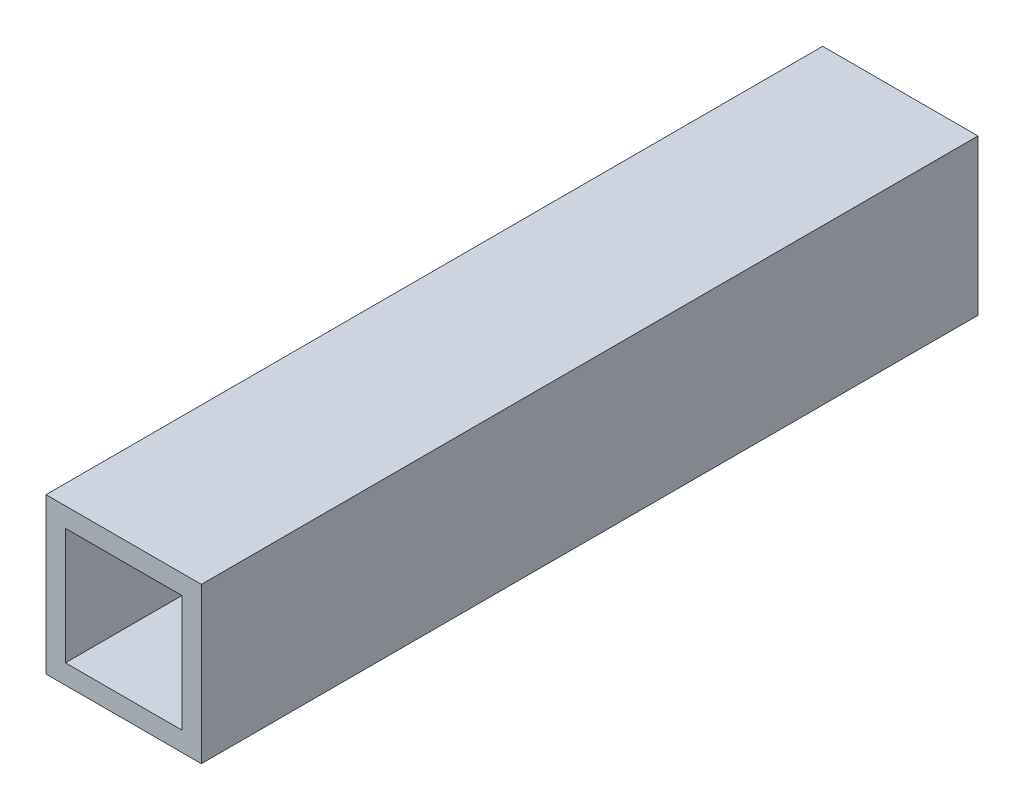
SolidWorks part; units mm, degrees
ref_plane "Front Plane" through (0, 0, 0) normal (0, 0, 1) x (1, 0, 0)
ref_plane "Top Plane" through (0, 0, 0) normal (0, 1, 0) x (1, 0, 0)
ref_plane "Right Plane" through (0, 0, 0) normal (1, 0, 0) x (0, 0, -1)
sketch "Sketch1" plane through (0, 0, 0) normal (0, 0, 1) x (1, 0, 0)
  line L1 (12.7, -12.7) -> (-12.7, -12.7)
  line L2 (12.7, -12.7) -> (12.7, 12.7)
  line L3 (12.7, 12.7) -> (-12.7, 12.7)
  line L4 (-12.7, -12.7) -> (-12.7, 12.7)
  line L5 (12.7, -12.7) -> (-12.7, 12.7) construction
  line L6 (12.7, 12.7) -> (-12.7, -12.7) construction
  point P0 (0, 0)
extrude "Boss-Extrude1" add sketch "Sketch1" along normal blind 127
sketch3d "3DSketch1"
  line L0 (-9.525, -9.525, 127) -> (9.525, -9.525, 127)
  line L1 (9.525, -9.525, 127) -> (9.525, 9.525, 127)
  line L2 (9.525, 9.525, 127) -> (-9.525, 9.525, 127)
  line L3 (-9.525, 9.525, 127) -> (-9.525, -9.525, 127)
  line L4 (-9.525, -9.525, 127) -> (9.525, -9.525, 127)
  line L5 (9.525, -9.525, 127) -> (9.525, 9.525, 127)
  line L6 (9.525, 9.525, 127) -> (-9.525, 9.525, 127)
  line L7 (-9.525, 9.525, 127) -> (-9.525, -9.525, 127)
  dimension "D1" = 3.175
extrude "Cut-Extrude1" cut sketch "3DSketch1" along direction (0, 0, 1) on the side of the normal blind 127 contours L4 L5 L6 L7
